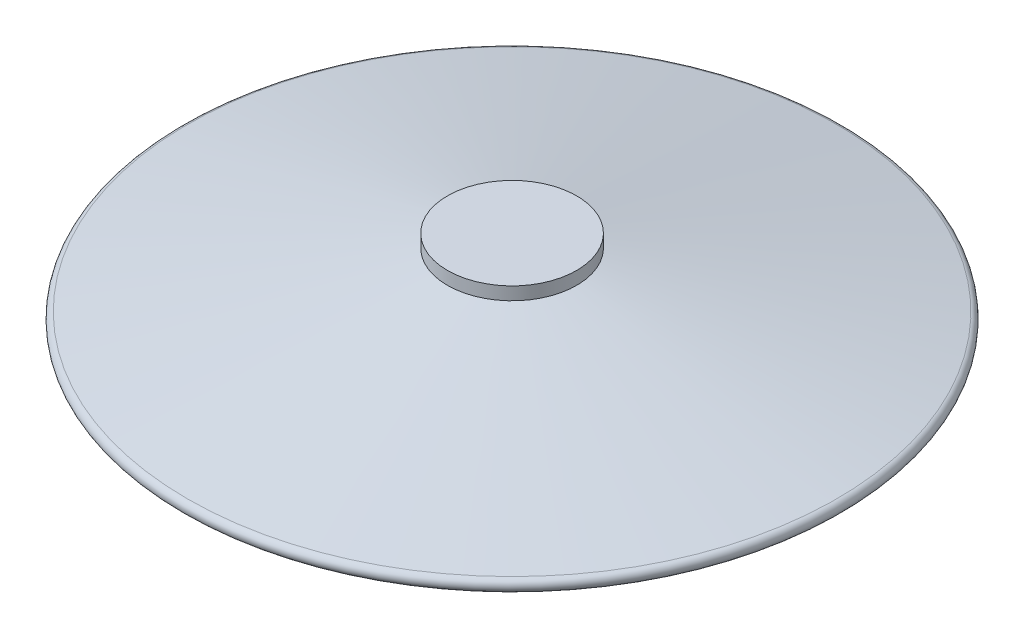
SolidWorks part; units mm, degrees
ref_plane "Front Plane" through (0, 0, 0) normal (0, 0, 1) x (1, 0, 0)
ref_plane "Top Plane" through (0, 0, 0) normal (0, 1, 0) x (1, 0, 0)
ref_plane "Right Plane" through (0, 0, 0) normal (1, 0, 0) x (0, 0, -1)
sketch "Sketch1" plane through (0, 0, 0) normal (0, 0, 1) x (1, 0, 0)
  line L0 (0, 17.7202) -> (0, -7.3937) construction
  line L1 (0, 6.25) -> (-5, 6.25)
  line L2 (-5, 6.25) -> (-5, 5.25)
  line L3 (-5, 5.25) -> (-25.1037, 0.9891)
  line L4 (-25, 0) -> (0, 0)
  line L5 (0, 6.25) -> (0, 0)
  arc A0 (-25.1037, 0.9891) -> (-25, 0) centre (-25, 0.5) ccw
  dimension "D1" = 0.5
  dimension "D2" = 50
  dimension "D3" = 10
  dimension "D4" = 1
  dimension "D5" = 6.25
revolve "Revolve1" add sketch "Sketch1" angle 360 about L0
sketch "Sketch2" plane through (0, 0, 0) normal (0, 0, 1) x (1, 0, 0)
  line L0 (0, 17.611) -> (0, -10.035) construction
